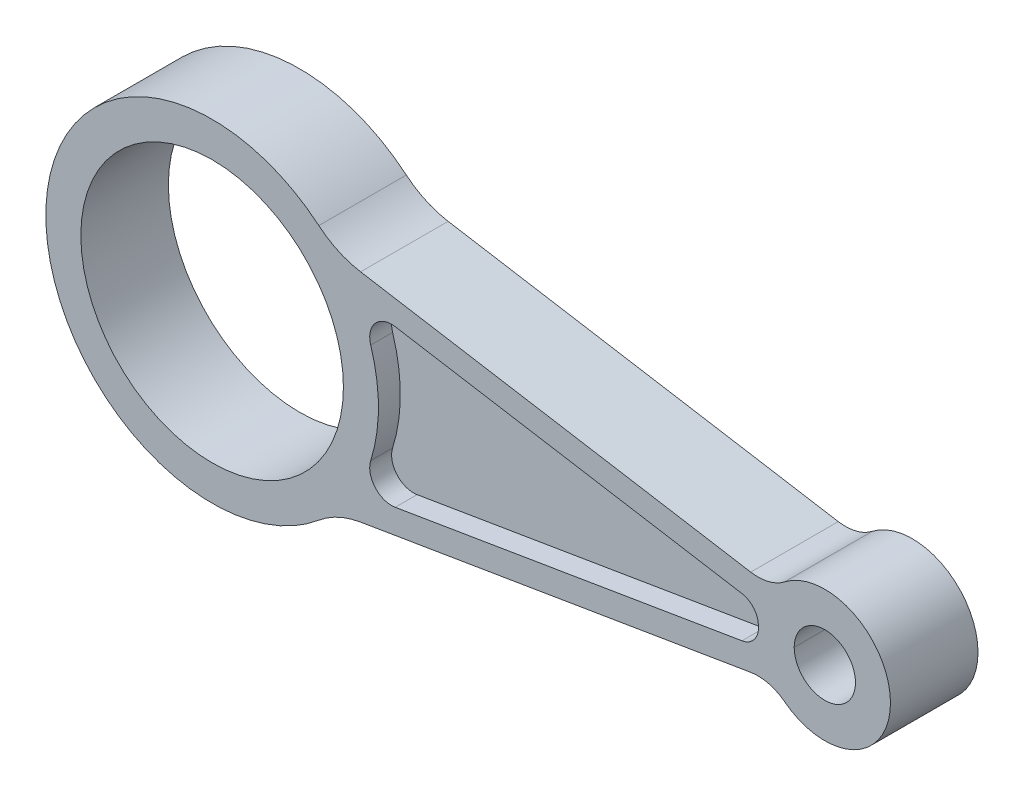
SolidWorks part; units mm, degrees
ref_plane "Front" through (0, 0, 0) normal (0, 0, 1) x (1, 0, 0)
ref_plane "Top" through (0, 0, 0) normal (0, 1, 0) x (1, 0, 0)
ref_plane "Right" through (0, 0, 0) normal (1, 0, 0) x (0, 0, -1)
other "Configuration Table"
sketch "Sketch1" plane through (0, 0, 0) normal (0, 0, 1) x (1, 0, 0)
  line L0 (-42.1775, 0) -> (237.8949, 0) construction
  line L1 (27.9355, 25.7606) -> (128.0638, 9.0844)
  line L2 (27.9355, -25.7606) -> (128.0638, -9.0844)
  arc A0 (27.9355, 25.7606) -> (27.9355, -25.7606) centre (0, 0) ccw
  arc A1 (128.0638, -9.0844) -> (128.0638, 9.0844) centre (140, 0) ccw
  circle A2 centre (0, 0) radius 30
  circle A3 centre (140, 0) radius 7
  dimension "D1" = 76
  dimension "D3" = 60
  dimension "D4" = 14
  dimension "D5" = 30
  dimension "D2" = 140
extrude "Base-Extrude" add sketch "Sketch1" against normal blind 20
fillet "Fillet1" radius 10 2 edges at (128.0638, 9.0844, -10) (128.0638, -9.0844, -10)
fillet "Fillet2" radius 20 2 edges at (27.9355, 25.7606, -10) (27.9355, -25.7606, -10)
sketch "Sketch2" plane through (0, 0, 0) normal (0, 0, 1) x (1, 0, 0)
  line L0 (41.8286, 17.871) -> (121.0469, 4.6773)
  line L1 (123.0688, 9.9163) -> (33.9231, 24.7634) construction
  line L2 (41.8286, -17.871) -> (121.0718, -4.6731)
  line L3 (33.9231, -24.7634) -> (123.0688, -9.9163) construction
  arc A0 (36.2389, -11.4344) -> (36.2389, 11.4344) centre (0, 0) ccw
  arc A3 (36.2389, 11.4344) -> (41.8286, 17.871) centre (41.0071, 12.9389) cw
  arc A4 (41.8286, -17.871) -> (36.2389, -11.4344) centre (41.0071, -12.9389) cw
  arc A5 (124.8077, 0.2384) -> (121.0469, 4.6773) centre (120.3077, 0.2384) ccw
  arc A6 (124.8077, 0.2384) -> (121.0718, -4.6731) centre (120.3325, -0.2343) cw
  dimension "D1" = 76
  dimension "D5" = 5
  dimension "D6" = 5
  dimension "D7" = 4.5
  dimension "D8" = 4.5
  dimension "D3" = 5.5
  dimension "D4" = 5.5
extrude "Cut-Extrude1" cut sketch "Sketch2" against normal blind 5
sketch "Sketch3" plane through (0, 0, -20) normal (0, 0, -1) x (-1, 0, 0)
  line L0 (-121.4456, 4.6109) -> (-41.8286, 17.871)
  line L1 (-123.0688, 9.9163) -> (-33.9231, 24.7634) construction
  line L2 (-121.4335, -4.6129) -> (-41.8286, -17.871)
  line L3 (-33.9231, -24.7634) -> (-123.0688, -9.9163) construction
  arc A0 (-36.2389, 11.4344) -> (-36.2389, -11.4344) centre (0, 0) ccw
  arc A1 (-41.8286, 17.871) -> (-36.2389, 11.4344) centre (-41.0071, 12.9389) cw
  arc A3 (-125.1942, -0.1579) -> (-121.4456, 4.6109) centre (-120.7063, 0.172) cw
  arc A4 (-125.1942, -0.1579) -> (-121.4335, -4.6129) centre (-120.6942, -0.174) ccw
  arc A5 (-41.8286, -17.871) -> (-36.2389, -11.4344) centre (-41.0071, -12.9389) ccw
  dimension "D1" = 76
  dimension "D2" = 5
  dimension "D5" = 4.5
  dimension "D6" = 4.5
  dimension "D7" = 5
  dimension "D3" = 5.5
  dimension "D4" = 5.5
extrude "Cut-Extrude2" cut sketch "Sketch3" against normal blind 5
split line "Split Line1"
